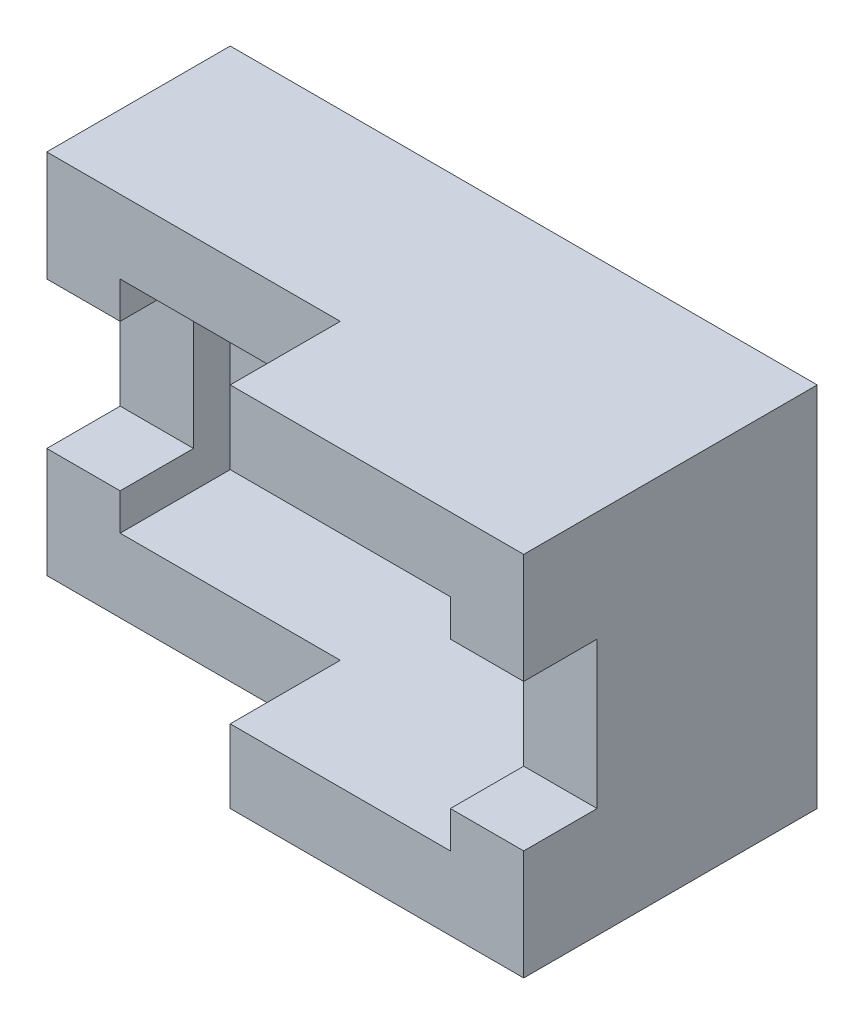
SolidWorks part; units mm, degrees
ref_plane "Front Plane" through (0, 0, 0) normal (0, 0, 1) x (1, 0, 0)
ref_plane "Top Plane" through (0, 0, 0) normal (0, 1, 0) x (1, 0, 0)
ref_plane "Right Plane" through (0, 0, 0) normal (1, 0, 0) x (0, 0, -1)
sketch "Sketch1" plane through (0, 0, 0) normal (0, 0, 1) x (1, 0, 0)
  line L1 (0, 0) -> (160, 0)
  line L2 (0, 0) -> (0, 100)
  line L3 (0, 100) -> (160, 100)
  line L4 (160, 0) -> (160, 100)
  dimension "D1" = 160
  dimension "D2" = 100
extrude "Boss-Extrude1" add sketch "Sketch1" along normal blind 50
sketch "Sketch2" plane through (0, 0, 50) normal (0, 0, 1) x (1, 0, 0)
  line L0 (0, 100) -> (0, 0) construction
  line L1 (0, 70) -> (20, 70)
  line L2 (0, 70) -> (0, 30)
  line L3 (0, 30) -> (20, 30)
  line L4 (20, 70) -> (20, 30)
  line L5 (160, 0) -> (160, 100) construction
  line L6 (160, 70) -> (140, 70)
  line L7 (160, 70) -> (160, 30)
  line L8 (160, 30) -> (140, 30)
  line L9 (140, 70) -> (140, 30)
  dimension "D1" = 20
  dimension "D2" = 40
  dimension "D3" = 20
  dimension "D4" = 40
  dimension "D5" = 30
  dimension "D6" = 30
extrude "Cut-Extrude1" cut sketch "Sketch2" against normal blind 20
sketch "Sketch3" plane through (0, 0, 0) normal (0, 0, -1) x (-1, 0, 0)
  line L1 (-40, 60) -> (-70, 60)
  line L2 (-40, 60) -> (-40, 40)
  line L3 (-40, 40) -> (-70, 40)
  line L4 (-70, 60) -> (-70, 40)
  line L5 (-90, 60) -> (-120, 60)
  line L6 (-90, 60) -> (-90, 40)
  line L7 (-90, 40) -> (-120, 40)
  line L8 (-120, 60) -> (-120, 40)
  dimension "D1" = 30
  dimension "D2" = 30
  dimension "D3" = 20
  dimension "D4" = 20
  dimension "D5" = 20
  dimension "D6" = 40
  dimension "D7" = 40
  dimension "D8" = 40
extrude "Cut-Extrude2" cut sketch "Sketch3" against normal blind 20
sketch "Sketch4" plane through (0, 0, 50) normal (0, 0, 1) x (1, 0, 0)
  line L1 (140, 80) -> (20, 80)
  line L2 (140, 80) -> (140, 20)
  line L3 (140, 20) -> (20, 20)
  line L4 (20, 80) -> (20, 20)
  dimension "D1" = 20
  dimension "D2" = 20
  dimension "D3" = 20
  dimension "D4" = 20
extrude "Cut-Extrude3" cut sketch "Sketch4" against normal blind 30
sketch "Sketch5" plane through (0, 0, 50) normal (0, 0, 1) x (1, 0, 0)
  line L0 (80, 100) -> (80, 80)
  line L1 (160, 100) -> (0, 100) construction
  line L2 (140, 80) -> (20, 80) construction
  line L3 (80, 80) -> (140, 80)
  line L4 (140, 80) -> (140, 70)
  line L5 (140, 70) -> (160, 70)
  line L6 (160, 70) -> (160, 100)
  line L7 (160, 100) -> (80, 100)
  line L8 (80, 0) -> (80, 20)
  line L9 (0, 0) -> (160, 0) construction
  line L10 (20, 20) -> (140, 20) construction
  line L11 (80, 20) -> (140, 20)
  line L12 (140, 20) -> (140, 30)
  line L13 (140, 30) -> (160, 30)
  line L14 (160, 30) -> (160, 0)
  line L15 (160, 0) -> (80, 0)
  dimension "D1" = 80
extrude "Boss-Extrude2" add sketch "Sketch5" along normal blind 30
sketch "Sketch8" plane through (140, 0, 0) normal (-1, 0, 0) x (0, 0, 1)
  line L0 (60, 70) -> (60, 30)
  line L1 (30, 70) -> (80, 70) construction
  line L2 (30, 30) -> (80, 30) construction
  line L3 (60, 70) -> (30, 70)
  line L4 (30, 70) -> (30, 30) construction
  line L5 (30, 70) -> (30, 30)
  line L6 (30, 30) -> (60, 30)
  dimension "D1" = 20
extrude "Boss-Extrude3" add sketch "Sketch8" against normal blind 20
